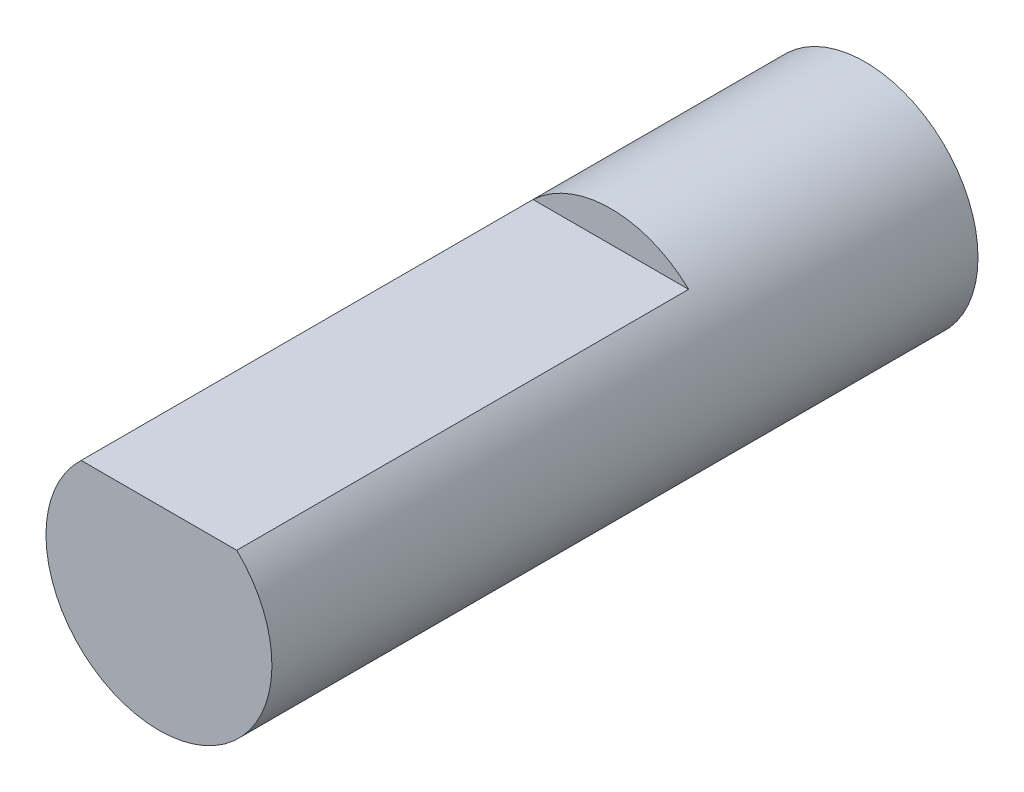
SolidWorks part; units mm, degrees
material "Plain Carbon Steel"
ref_plane "Front" through (0, 0, 0) normal (0, 0, 1) x (1, 0, 0)
ref_plane "Top" through (0, 0, 0) normal (0, 1, 0) x (1, 0, 0)
ref_plane "Right" through (0, 0, 0) normal (1, 0, 0) x (0, 0, -1)
sketch "Sketch1" plane through (0, 0, 0) normal (0, 0, 1) x (1, 0, 0)
  circle A0 centre (0, 0) radius 2
  dimension "D1" = 4
extrude "Boss-Extrude1" add sketch "Sketch1" along normal blind 12.5
sketch "Sketch2" plane through (0, 0, 12.5) normal (0, 0, 1) x (1, 0, 0)
  line L0 (-1.3775, 1.45) -> (1.3775, 1.45)
  circle A1 centre (0, 0) radius 2
  arc A2 (1.3775, 1.45) -> (-1.3775, 1.45) centre (0, 0) ccw
  dimension "D2" = 1.45
  dimension "D1" = 0
extrude "Cut-Extrude1" cut sketch "Sketch2" against normal blind 8
